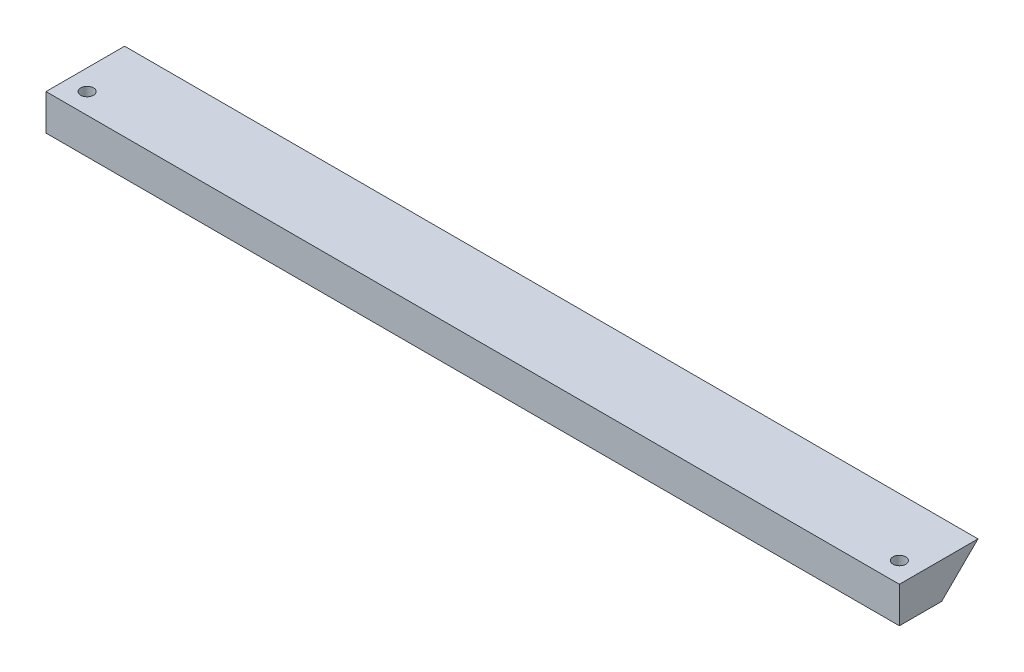
SolidWorks part; units mm, degrees
material "A286 Iron Base Superalloy"
ref_plane "Front Plane" through (0, 0, 0) normal (0, 0, 1) x (1, 0, 0)
ref_plane "Top Plane" through (0, 0, 0) normal (0, 1, 0) x (1, 0, 0)
ref_plane "Right Plane" through (0, 0, 0) normal (1, 0, 0) x (0, 0, -1)
sketch "Sketch2" plane through (0, 0, 0) normal (1, 0, 0) x (0, 0, -1)
  line L0 (0, 0) -> (15.29, 0)
  line L1 (15.29, 0) -> (8.22, -7)
  line L2 (8.22, -7) -> (0, -7)
  line L3 (0, -7) -> (0, 0)
  dimension "D1" = 15.29
  dimension "D2" = 7
  dimension "D3" = 8.22
  dimension "D4" = 9.9491
extrude "Boss-Extrude1" add sketch "Sketch2" along normal mid plane 166
sketch "Sketch3" plane through (0, -7, 0) normal (0, -1, 0) x (-1, 0, 0)
  line L0 (-83, 0) -> (83, 0) construction
  line L1 (83, 0) -> (83, 8.22) construction
  line L2 (-83, 0) -> (-83, 8.22) construction
  circle A0 centre (79, 4) radius 1.5
  circle A1 centre (-79, 4) radius 1.5
  dimension "D1" = 3
  dimension "D2" = 3
  dimension "D3" = 4
  dimension "D4" = 4
  dimension "D5" = 4
  dimension "D6" = 4
hole_wizard "M3x0.5 Tapped Hole1" positions "Sketch5" profile "Sketch4" tap size "M3x0.5" standard "ANSI Metric" end condition through all
sketch "Sketch5" plane through (0, -7, 0) normal (0, -1, 0) x (-1, 0, 0)
  point P0 (79, 4)
  point P3 (-79, 4)
sketch "Sketch4" plane through (-79, -7, -4) normal (1, 0, 0) x (0, 0, -1)
  line L0 (0, 0) -> (0, 7)
  line L1 (0, 7) -> (1.25, 7)
  line L2 (1.25, 7) -> (1.25, 0)
  line L5 (1.25, 0) -> (0, 0)
  line L11 (0, -6.35) -> (0, 107.95) construction
  dimension "Thru Tap Drill Dia." = 2.5
  dimension "Thru Tap Drill Depth" = 7
cosmetic thread "Hole Thread1" parameters "D2"=3
cosmetic thread "Hole Thread2" parameters "D2"=3
